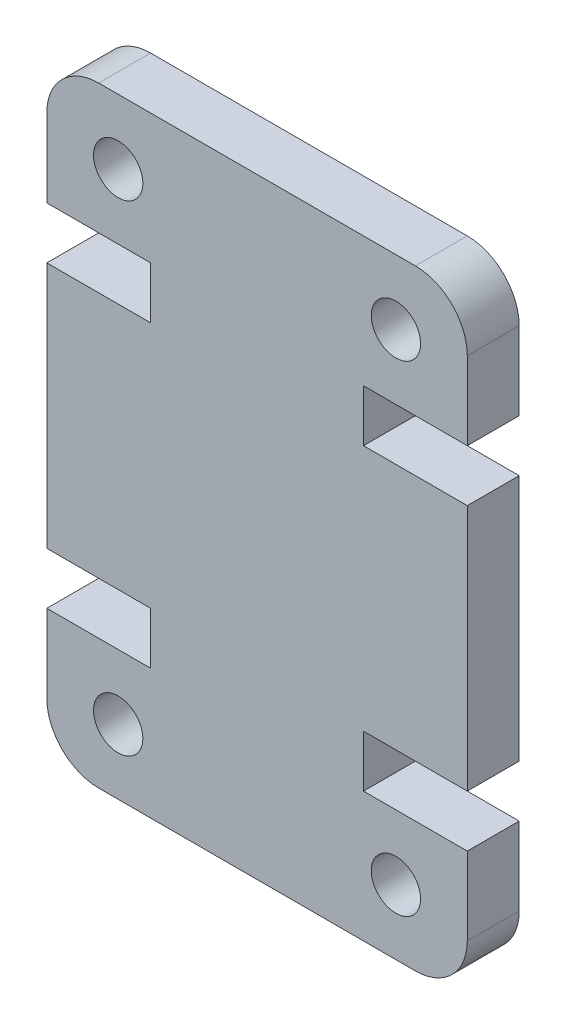
SolidWorks part; units mm, degrees
ref_plane "Front Plane" through (0, 0, 0) normal (0, 0, 1) x (1, 0, 0)
ref_plane "Top Plane" through (0, 0, 0) normal (0, 1, 0) x (1, 0, 0)
ref_plane "Right Plane" through (0, 0, 0) normal (1, 0, 0) x (0, 0, -1)
sketch "Sketch1" plane through (0, 0, 0) normal (0, 0, 1) x (1, 0, 0)
  line L0 (8.1, 23.525) -> (8.1, 0) construction
  line L1 (0, 11.7625) -> (16.2, 11.7625) construction
  line L2 (16.2, 5) -> (16.2, 2)
  line L3 (12.2, 5) -> (16.2, 5)
  line L4 (16.2, 7) -> (12.2, 7)
  line L5 (12.2, 7) -> (12.2, 5)
  line L6 (16.2, 7) -> (16.2, 16.525)
  line L7 (0, 18.525) -> (0, 21.525)
  line L8 (4, 18.525) -> (0, 18.525)
  line L9 (0, 16.525) -> (4, 16.525)
  line L10 (4, 16.525) -> (4, 18.525)
  line L11 (2, 23.525) -> (14.2, 23.525)
  line L12 (12.2, 16.525) -> (12.2, 18.525)
  line L13 (16.2, 16.525) -> (12.2, 16.525)
  line L14 (12.2, 18.525) -> (16.2, 18.525)
  line L15 (16.2, 18.525) -> (16.2, 21.525)
  line L20 (0, 7) -> (0, 16.525)
  line L23 (2, 0) -> (14.2, 0)
  line L30 (4, 7) -> (4, 5)
  line L32 (0, 7) -> (4, 7)
  line L33 (4, 5) -> (0, 5)
  line L39 (0, 5) -> (0, 2)
  circle A0 centre (13.45, 2.5) radius 0.95
  arc A2 (16.2, 2) -> (14.2, 0) centre (14.2, 2) cw
  circle A4 centre (2.75, 21.025) radius 0.95
  arc A5 (0, 21.525) -> (2, 23.525) centre (2, 21.525) cw
  arc A7 (16.2, 21.525) -> (14.2, 23.525) centre (14.2, 21.525) ccw
  circle A9 centre (13.45, 21.025) radius 0.95
  arc A11 (0, 2) -> (2, 0) centre (2, 2) ccw
  circle A13 centre (2.75, 2.5) radius 0.95
  point P18 (8.1, 11.7625)
  dimension "D2" = 2
  dimension "D4" = 1.9
  dimension "D3" = 2.75
  dimension "D5" = 8.1
  dimension "D6" = 2.5
  dimension "D7" = 5
  dimension "D10" = 11.7625
extrude "Boss-Extrude1" add sketch "Sketch1" along normal blind 2
equation "\"D10@Sketch1\"= ( \"HL@parametersSketch@prostheticParameters.SLDPRT\" * 0.165 - 3 - 4 ) / 2 'MIP length - Sil. Sht MIP - Sil. Sht DIP"
equation "\"D5@Sketch1\"= \"fingerWidth@parametersSketch@prostheticParameters.SLDPRT\" / 2'MIP width"
equation "\"D4@Sketch1\"= 1.5 + \"tol1@parametersSketch@prostheticParameters.SLDPRT\""
